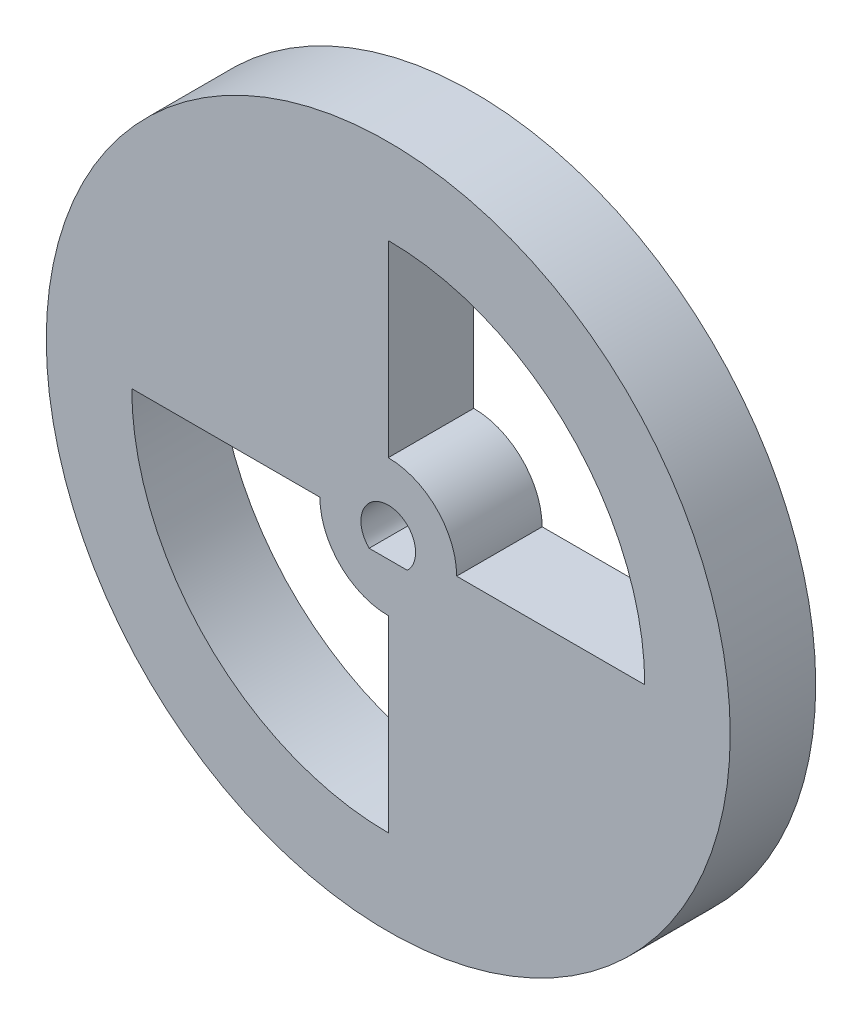
SolidWorks part; units mm, degrees
ref_plane "Plano frontal" through (0, 0, 0) normal (0, 0, 1) x (1, 0, 0)
ref_plane "Plano superior" through (0, 0, 0) normal (0, 1, 0) x (1, 0, 0)
ref_plane "Plano direito" through (0, 0, 0) normal (1, 0, 0) x (0, 0, -1)
ref_plane "Plano1" through (0, 0, 0) normal (0, 0, -1) x (-1, 0, 0)
sketch "Esboço1" plane through (0, 0, 0) normal (0, 0, -1) x (-1, 0, 0)
  line L0 (47.6452, 19) -> (49.8812, 19)
  line L141 (48.7632, 24.1446) -> (48.7632, 35.1446)
  line L142 (48.7632, 5.1446) -> (48.7632, 16.1446)
  line L143 (63.7632, 20.1446) -> (52.7632, 20.1446)
  line L144 (44.7632, 20.1446) -> (33.7632, 20.1446)
  arc A1 (48.7632, 16.1446) -> (52.7632, 20.1446) centre (48.7632, 20.1446) ccw
  arc A2 (48.7632, 5.1446) -> (63.7632, 20.1446) centre (48.7632, 20.1446) ccw
  circle A3 centre (48.7632, 20.1446) radius 20
  arc A4 (48.7632, 35.1446) -> (33.7632, 20.1446) centre (48.7632, 20.1446) ccw
  arc A5 (48.7632, 24.1446) -> (44.7632, 20.1446) centre (48.7632, 20.1446) ccw
  arc A6 (49.8812, 19) -> (47.6452, 19) centre (48.7632, 20.1446) ccw
  point P149 (48.7632, 20.1446)
  point P152 (48.7632, 20)
  dimension "D1" = 40
  dimension "D3" = 3.2
extrude "Ressalto-extrusão1" add sketch "Esboço1" against normal blind 5
